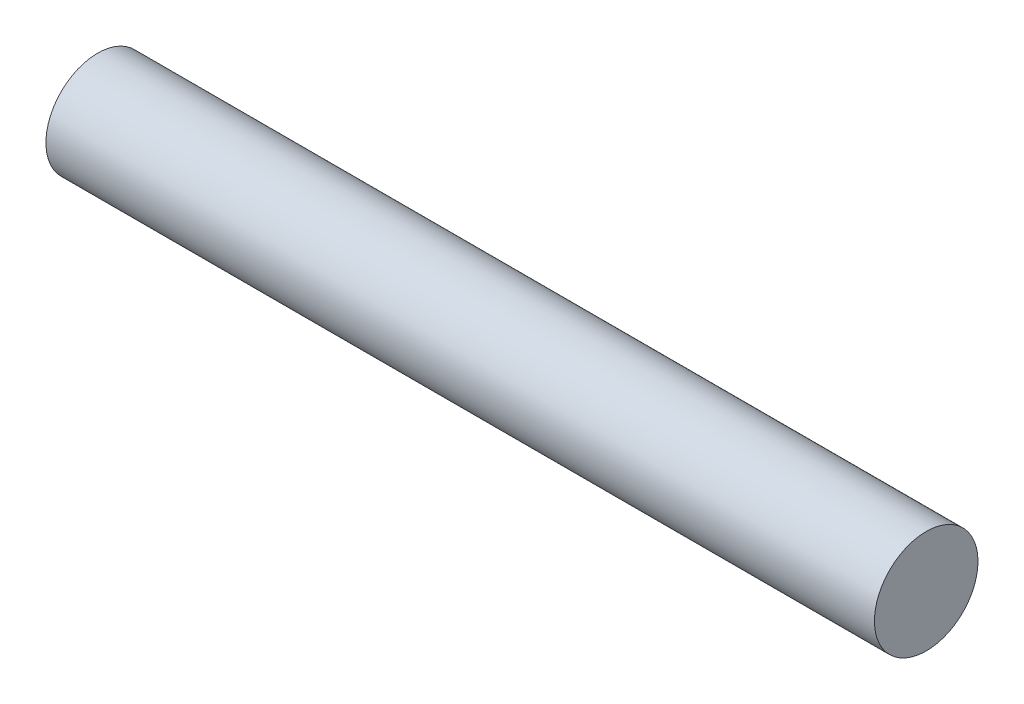
SolidWorks part; units mm, degrees
material "Ductile Iron (SN)"
ref_plane "Front Plane" through (0, 0, 0) normal (0, 0, 1) x (1, 0, 0)
ref_plane "Top Plane" through (0, 0, 0) normal (0, 1, 0) x (1, 0, 0)
ref_plane "Right Plane" through (0, 0, 0) normal (1, 0, 0) x (0, 0, -1)
sketch "Sketch1" plane through (0, 0, 0) normal (1, 0, 0) x (0, 0, -1)
  circle A0 centre (0, 0) radius 25
  dimension "D1" = 50
extrude "Boss-Extrude1" add sketch "Sketch1" along normal blind 400
